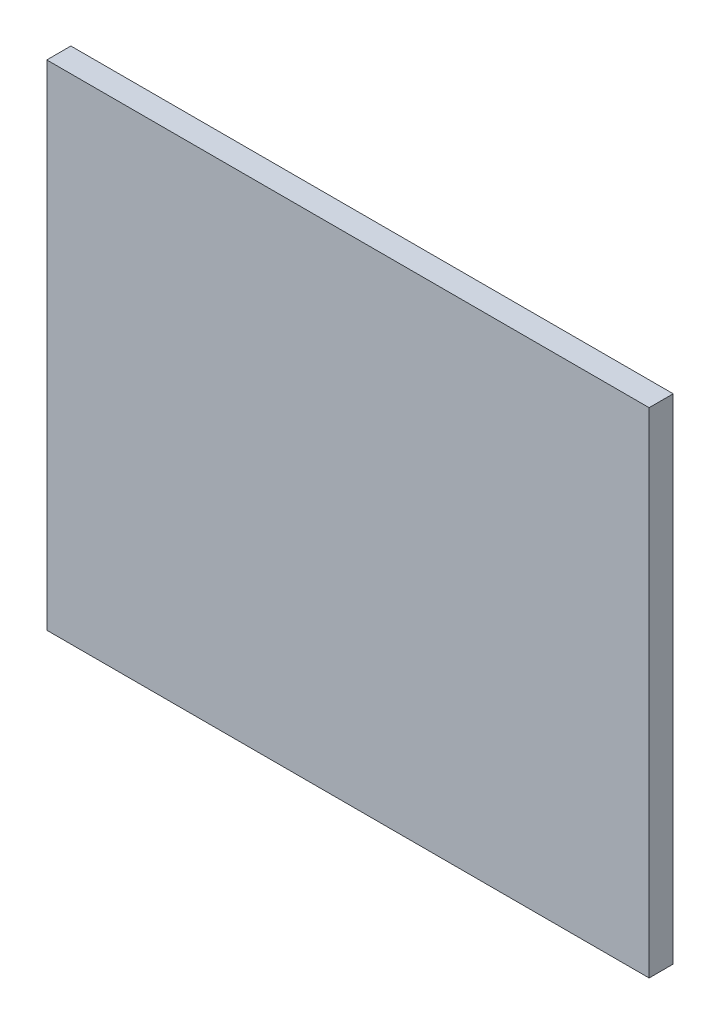
SolidWorks part; units mm, degrees
ref_plane "Front Plane" through (0, 0, 0) normal (0, 0, 1) x (1, 0, 0)
ref_plane "Top Plane" through (0, 0, 0) normal (0, 1, 0) x (1, 0, 0)
ref_plane "Right Plane" through (0, 0, 0) normal (1, 0, 0) x (0, 0, -1)
sketch "Sketch1" plane through (0, 0, 0) normal (0, 0, 1) x (1, 0, 0)
  line L1 (-5, -10.25) -> (20, -10.25)
  line L2 (-5, -10.25) -> (-5, 10.25)
  line L3 (-5, 10.25) -> (20, 10.25)
  line L4 (20, -10.25) -> (20, 10.25)
  point P0 (0, 0)
  point P6 (16, 10.25)
  dimension "D1" = 5
  dimension "D2" = 20.5
  dimension "D3" = 20
  dimension "D4" = 10.25
  dimension "D5" = 4
extrude "Boss-Extrude1" add sketch "Sketch1" along normal blind 1
sketch "Sketch2" plane through (0, 10.25, 0) normal (0, 1, 0) x (1, 0, 0)
  line L0 (20, -1) -> (-5, -1) construction
  point P0 (7.5, -1)
